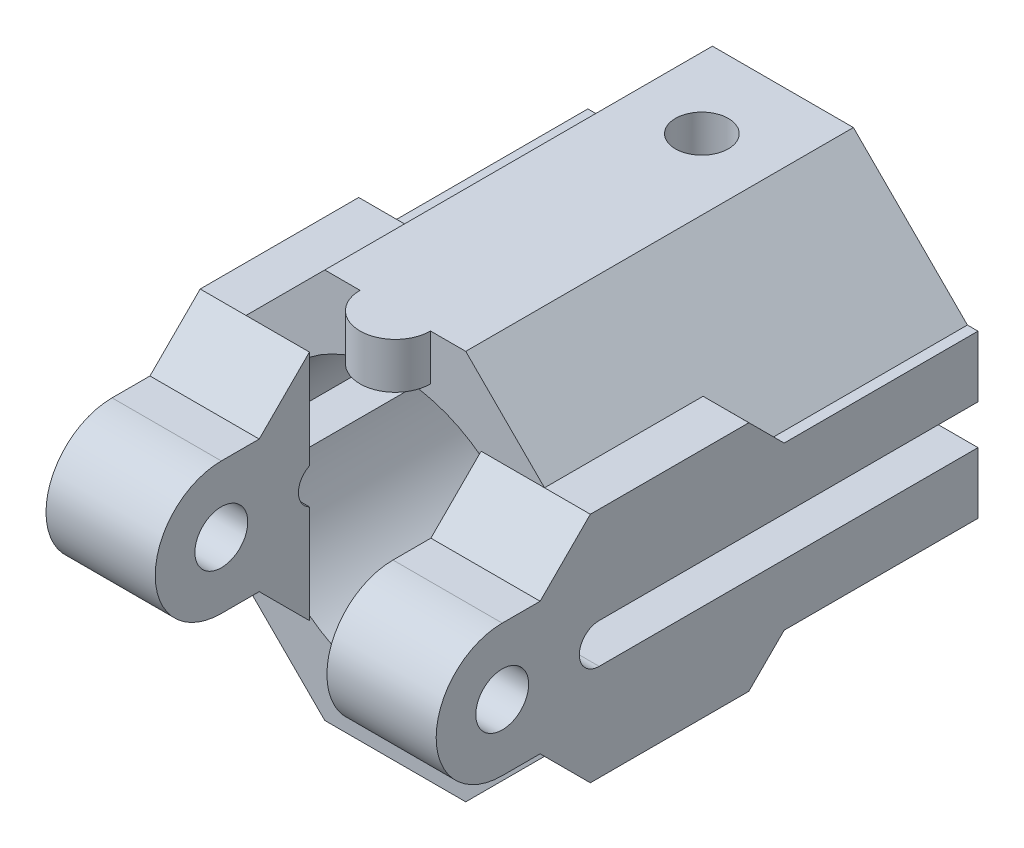
SolidWorks part; units mm, degrees
ref_plane "Front Plane" through (0, 0, 0) normal (0, 0, 1) x (1, 0, 0)
ref_plane "Top Plane" through (0, 0, 0) normal (0, 1, 0) x (1, 0, 0)
ref_plane "Right Plane" through (0, 0, 0) normal (1, 0, 0) x (0, 0, -1)
sketch "Sketch1" plane through (0, 0, 0) normal (0, 0, 1) x (1, 0, 0)
  line L0 (-11.0711, 4) -> (-11.0711, -4)
  line L1 (11.0711, 4) -> (11.0711, -4)
  line L2 (-4, -11.0711) -> (4, -11.0711)
  line L3 (-4, 11.0711) -> (4, 11.0711)
  line L4 (-1000, 0) -> (49000, 0) construction
  line L5 (0, -1000) -> (0, 49000) construction
  line L6 (-11.0711, -4) -> (-4, -11.0711)
  line L7 (-11.0711, 4) -> (-4, 11.0711)
  line L8 (4, 11.0711) -> (11.0711, 4)
  line L9 (11.0711, -4) -> (4, -11.0711)
  circle A0 centre (0, 0) radius 8
  dimension "D1" = 16
  dimension "D2" = 4
  dimension "D3" = 8
  dimension "D4" = 8
  dimension "D5" = 4
  dimension "D6" = 8
  dimension "D7" = 4
  dimension "D8" = 8
  dimension "D9" = 4
  dimension "D10" = 45
  dimension "D11" = 10
  dimension "D12" = 45
  dimension "D13" = 45
extrude "Boss-Extrude1" add sketch "Sketch1" along normal blind 22
sketch "Sketch2" plane through (11.0711, 0, 0) normal (1, 0, 0) x (0, 0, -1)
  line L0 (0, -4) -> (0, 4) construction
  line L1 (0, -4.6) -> (-11, -4.6)
  line L2 (0, -4.6) -> (0, 4.6)
  line L3 (0, 4.6) -> (-11, 4.6)
  line L4 (-11, -4.6) -> (-11, 4.6) construction
  line L5 (-11, -4.6) -> (-13.0058, -6.6)
  line L6 (-11, 6.6) -> (-30, 6.6) construction
  line L7 (-11, 6.6) -> (-11, -6.6) construction
  line L8 (-11, -6.6) -> (-30, -6.6) construction
  line L9 (-30, 6.6) -> (-30, -6.6) construction
  line L10 (-11, 4.6) -> (-13.0029, 6.6)
  line L11 (-22, 6.6) -> (-24.85, 3.75)
  line L12 (-13.0058, 4.6) -> (-22.0058, 4.6) construction
  line L13 (-11, 4.6) -> (-11, -4.6) construction
  line L14 (-13.0058, 4.6) -> (-13.0058, -4.6) construction
  line L15 (-13.0058, -4.6) -> (-22.0058, -4.6) construction
  line L16 (-22.0058, 4.6) -> (-22.0058, -4.6) construction
  line L17 (-22, 4) -> (-22, 11.0711) construction
  line L18 (-22, -6.6) -> (-24.85, -3.75)
  line L19 (-22, -11.0711) -> (-22, -4) construction
  line L20 (-1000, 0) -> (49000, 0) construction
  line L21 (-27, 3.75) -> (-22.0058, 3.75)
  line L22 (-27, -3.75) -> (-22.0058, -3.75)
  line L23 (-22, -6.6) -> (-13.0058, -6.6)
  line L24 (-22, 6.6) -> (-13.0029, 6.6)
  circle A0 centre (-27, 0) radius 3.75
  circle A1 centre (-27, 0) radius 1.5
  dimension "D17" = 3
  dimension "D18" = 7.5
  dimension "D1" = 11
  dimension "D2" = 9.2
  dimension "D3" = 4.6
  dimension "D4" = 19
  dimension "D5" = 0
  dimension "D6" = 13.2
  dimension "D7" = 6.6
  dimension "D8" = 9
  dimension "D9" = 0
  dimension "D10" = 4.6
  dimension "D11" = 9.2
  dimension "D12" = 0
  dimension "D13" = 45
  dimension "D14" = 45
  dimension "D15" = 0
  dimension "D16" = 0
  dimension "D19" = 27
extrude "Boss-Extrude3" add sketch "Sketch2" against normal blind 6.2
sketch "Sketch6" plane through (-11.0711, 0, 0) normal (-1, 0, 0) x (0, 0, 1)
  line L0 (11, -4.7491) -> (0, -4.7491)
  line L1 (0, -4.7491) -> (0, 4.4509)
  line L2 (11, 4.4509) -> (0, 4.4509)
  line L22 (0, 11.0711) -> (0, 4) construction
  line L23 (22.0058, 4.6) -> (22.0058, -4.6) construction
  line L24 (13.0058, -4.6) -> (22.0058, -4.6) construction
  line L25 (13.0058, 4.6) -> (13.0058, -4.6) construction
  line L26 (11, 4.4509) -> (11, -4.7491) construction
  line L27 (13.0058, 4.6) -> (22.0058, 4.6) construction
  line L28 (30, 6.6) -> (30, -6.6) construction
  line L29 (11, -6.6) -> (30, -6.6) construction
  line L30 (11, 6.6) -> (11, -6.6) construction
  line L31 (11, 6.6) -> (30, 6.6) construction
  line L32 (11, -4.7491) -> (11, 4.4509) construction
  line L33 (22, 6.6) -> (13.0029, 6.6)
  line L34 (22, -6.6) -> (13.0058, -6.6)
  line L35 (27, -3.75) -> (22.0058, -3.75)
  line L36 (27, 3.75) -> (22.0058, 3.75)
  line L37 (22, -6.6) -> (24.85, -3.75)
  line L38 (22, 6.6) -> (24.85, 3.75)
  line L39 (11, 4.4509) -> (13.0029, 6.6)
  line L40 (11, -4.7491) -> (13.0058, -6.6)
  circle A2 centre (27, 0) radius 1.5
  circle A3 centre (27, 0) radius 3.75
  dimension "D2" = 9.2
extrude "Boss-Extrude4" add sketch "Sketch6" against normal blind 6.2
sketch "Sketch7" plane through (11.0711, 0, 0) normal (1, 0, 0) x (0, 0, -1)
  line L0 (0, -4.6) -> (0, 4.6) construction
  line L1 (0, 1.125) -> (-21.5, 1.125)
  line L2 (0, 1.125) -> (0, -1.125)
  line L3 (0, -1.125) -> (-21.5, -1.125)
  line L4 (-21.5, 1.125) -> (-21.5, -1.125)
  circle A0 centre (-21.5, 0) radius 1.125
  line M4 (0, -4.6) -> (0, 4.6)
  dimension "D1" = 21.5
  dimension "D2" = 1.125
  dimension "D3" = 2.25
extrude "Cut-Extrude2" cut sketch "Sketch7" against normal blind 30 contours A0 L3 L1 M4 | L4 A0 | L4 A0
sketch "Sketch8" plane through (0, 11.0711, 0) normal (0, 1, 0) x (1, 0, 0)
  circle A0 centre (0, -4.6) radius 1.5
  dimension "D1" = 3
  dimension "D2" = 4.6
extrude "Cut-Extrude3" cut sketch "Sketch8" against normal blind 30
sketch "Sketch9" plane through (0, 0, 0) normal (0, 0, -1) x (-1, 0, 0)
  circle A0 centre (0, 0) radius 8
extrude "Cut-Extrude4" cut sketch "Sketch9" against normal blind 22
sketch "Sketch10" plane through (0, 11.0711, 0) normal (0, 1, 0) x (1, 0, 0)
  line L0 (0, -1000) -> (0, 49000) construction
  line L1 (4, -22) -> (-4, -22) construction
  circle A0 centre (0, -22) radius 2
  dimension "D1" = 4
extrude "Boss-Extrude5" add sketch "Sketch10" against normal blind 2.6
sketch "Sketch11" plane through (0, -11.0711, 0) normal (0, -1, 0) x (1, 0, 0)
  line L0 (-4, 22) -> (-4, 0) construction
  line L1 (-2.6, 18.4) -> (2.6, 18.4)
  line L2 (-2.6, 18.4) -> (-2.6, 11.9)
  line L3 (-2.6, 11.9) -> (2.6, 11.9)
  line L4 (2.6, 18.4) -> (2.6, 11.9)
  line L5 (4, 22) -> (4, 0) construction
  line L6 (-4, 22) -> (4, 22) construction
  circle A0 centre (0, 18.4) radius 2.6
  circle A1 centre (0, 11.9) radius 2.6
  dimension "D1" = 1.4
  dimension "D2" = 6.5
  dimension "D3" = 1.4
  dimension "D4" = 3.6
extrude "Cut-Extrude5" cut sketch "Sketch11" against normal blind 1 contours L1 A0 | A1 L4 A0 L2 | L3 A1 | L3 A1 | L1 A0
